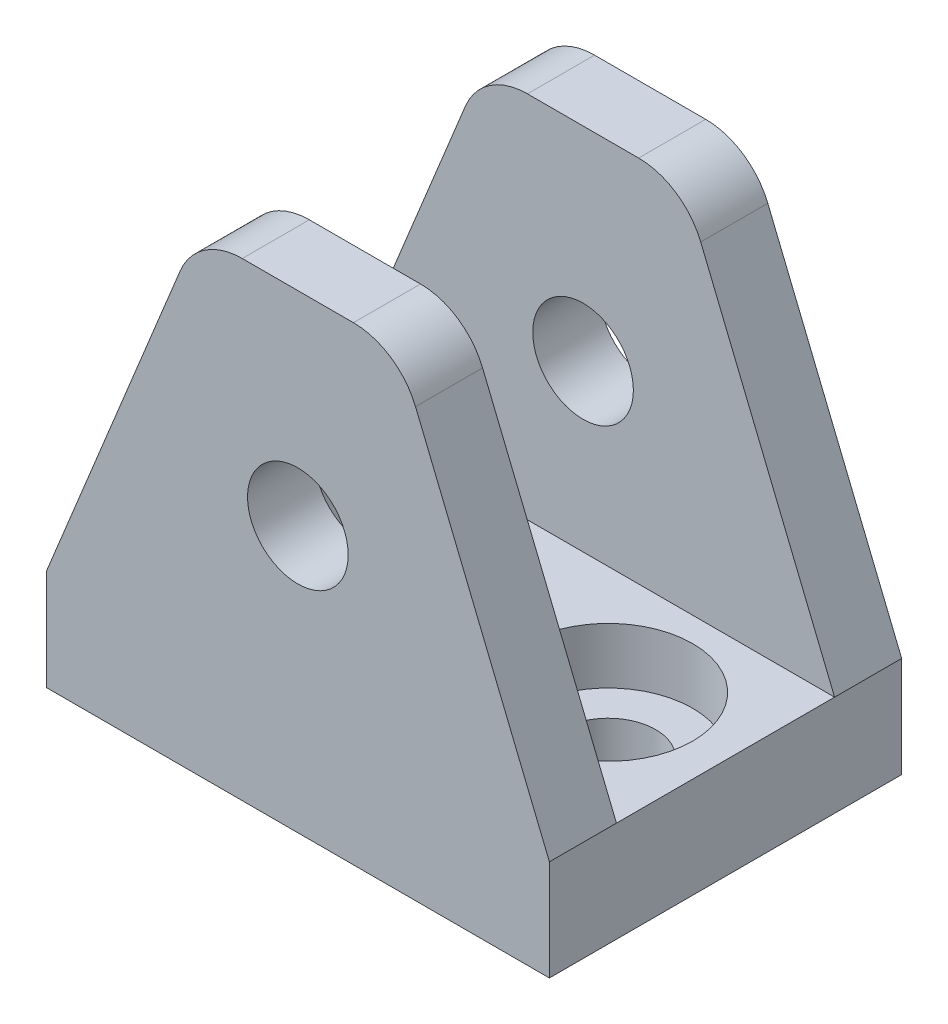
SolidWorks part; units mm, degrees
material "6061-T6 (SS)"
ref_plane "X-Y Datum" through (0, 0, 0) normal (0, 0, 1) x (1, 0, 0)
ref_plane "X-Z Datum" through (0, 0, 0) normal (0, 1, 0) x (1, 0, 0)
ref_plane "Y-Z Datum" through (0, 0, 0) normal (1, 0, 0) x (0, 0, -1)
sketch "Sketch1" plane through (0, 0, 0) normal (0, 1, 0) x (1, 0, 0)
  line L1 (-23.8125, -16.6751) -> (23.8125, -16.6751)
  line L2 (-23.8125, -16.6751) -> (-23.8125, 16.6751)
  line L3 (-23.8125, 16.6751) -> (23.8125, 16.6751)
  line L4 (23.8125, -16.6751) -> (23.8125, 16.6751)
  line L5 (-23.8125, -16.6751) -> (23.8125, 16.6751) construction
  line L6 (-23.8125, 16.6751) -> (23.8125, -16.6751) construction
  point P0 (0, 0)
  dimension "D1" = 47.625
  dimension "D2" = 33.3502
extrude "Boss-Extrude1" add sketch "Sketch1" along normal blind 44.45
sketch "Sketch2" plane through (0, 44.45, 0) normal (0, 1, 0) x (1, 0, 0)
  line L0 (23.8125, -16.6751) -> (23.8125, 16.6751) construction
  line L1 (-23.8125, -10.3251) -> (23.8125, -10.3251)
  line L2 (-23.8125, -10.3251) -> (-23.8125, 10.3251)
  line L3 (-23.8125, 10.3251) -> (23.8125, 10.3251)
  line L4 (23.8125, -10.3251) -> (23.8125, 10.3251)
  line L5 (-23.8125, -10.3251) -> (23.8125, 10.3251) construction
  line L6 (-23.8125, 10.3251) -> (23.8125, -10.3251) construction
  line L7 (23.8125, 16.6751) -> (-23.8125, 16.6751) construction
  point P0 (0, 0)
  dimension "D1" = 6.35
extrude "Cut-Extrude1" cut sketch "Sketch2" against normal offset from surface (34.925 mm away) 9.525 up to face at (0, 0, 0)
sketch "Sketch3" plane through (0, 0, -16.6751) normal (0, 0, -1) x (-1, 0, 0)
  line L9 (9.525, 44.45) -> (23.8125, 44.45)
  line L10 (-23.8125, 44.45) -> (23.8125, 44.45) construction
  line L11 (23.8125, 44.45) -> (23.8125, 9.525)
  line L12 (23.8125, 44.45) -> (23.8125, 0) construction
  line L13 (23.8125, 9.525) -> (9.525, 44.45)
  line L14 (-23.8125, 0) -> (23.8125, 0) construction
  line L15 (0, 0) -> (0, -50000) construction
  line L17 (-23.8125, 44.45) -> (-23.8125, 9.525)
  line L18 (-9.525, 44.45) -> (-23.8125, 44.45)
  line L19 (-23.8125, 9.525) -> (-9.525, 44.45)
  line M2 (23.8125, 0) -> (23.8125, 44.45)
  line M3 (23.8125, 44.45) -> (-23.8125, 44.45)
  line M4 (-23.8125, 44.45) -> (-23.8125, 0)
  dimension "D1" = 9.525
  dimension "D2" = 19.05
extrude "Cut-Extrude2" cut sketch "Sketch3" against normal through all and the other way through all contours L13 M2 M3 | L19 M4 M3
hole_wizard "CBORE for M8 Hex Head Bolt1" positions "Sketch6" profile "Sketch7" counterbore size "M8" standard "ANSI Metric"
sketch "Sketch6" plane through (0, 9.525, 0) normal (0, 1, 0) x (1, 0, 0)
  line L0 (0, 0) -> (0, 50000) construction
  line L1 (0, 0) -> (50000, 0) construction
  point P0 (-12.7, 0)
  point P2 (12.7, 0)
  dimension "D1" = 12.7
  dimension "D2" = 12.7
sketch "Sketch7" plane through (-12.7, 9.525, 0) normal (1, 0, 0) x (0, 0, 1)
  line L0 (0, 0) -> (0, 16.002)
  line L1 (0, 16.002) -> (4.5, 13.2981)
  line L2 (4.5, 13.2981) -> (4.5, 5.3)
  line L3 (4.5, 5.3) -> (8, 5.3)
  line L4 (8, 5.3) -> (8, 0)
  line L5 (8, 0) -> (0, 0)
  line L10 (0, 16.002) -> (-4.5, 13.2981) construction
  line L11 (0, -6.35) -> (0, 107.95) construction
  dimension "Hole Dia." = 9
  dimension "Hole Depth" = 16.002
  dimension "C'Bore Dia." = 16
  dimension "C'Bore Depth" = 5.3
  dimension "Drill Angle" = 118
sketch "Sketch8" plane through (0, 9.525, 0) normal (0, 1, 0) x (1, 0, 0)
  line L0 (-3.175, 0) -> (3.175, 0) construction
  line L1 (-3.175, 6.35) -> (3.175, 6.35)
  line L2 (-3.175, -6.35) -> (3.175, -6.35)
  arc A0 (-3.175, 6.35) -> (-3.175, -6.35) centre (-3.175, 0) ccw
  arc A1 (3.175, -6.35) -> (3.175, 6.35) centre (3.175, 0) ccw
  point P3 (0, 0)
  dimension "D2" = 6.35
  dimension "D1" = 6.35
fillet "Fillet3" radius 6.35 4 edges at (9.525, 44.45, 13.5001) (-9.525, 44.45, 13.5001) (9.525, 44.45, -13.5001) (-9.525, 44.45, -13.5001)
extrude "Cut-Extrude3" [suppressed] cut sketch "Sketch8" against normal through all
hole_wizard "3/8 (0.375) Diameter Hole1" positions "Sketch9" profile "Sketch11" hole size "3/8" standard "ANSI Inch" end condition through all
sketch "Sketch9" plane through (0, 0, 16.6751) normal (0, 0, 1) x (1, 0, 0)
  point P0 (0, 25.1617)
sketch "Sketch11" plane through (0, 25.1617, 16.6751) normal (1, 0, 0) x (0, -1, 0)
  line L0 (0, 0) -> (0, 33.3503)
  line L1 (0, 33.3503) -> (4.7625, 33.3503)
  line L2 (4.7625, 33.3503) -> (4.7625, 0)
  line L5 (4.7625, 0) -> (0, 0)
  line L11 (0, -6.35) -> (0, 107.95) construction
  dimension "Thru Hole Dia." = 9.525
  dimension "Thru Hole Depth" = 33.3503
